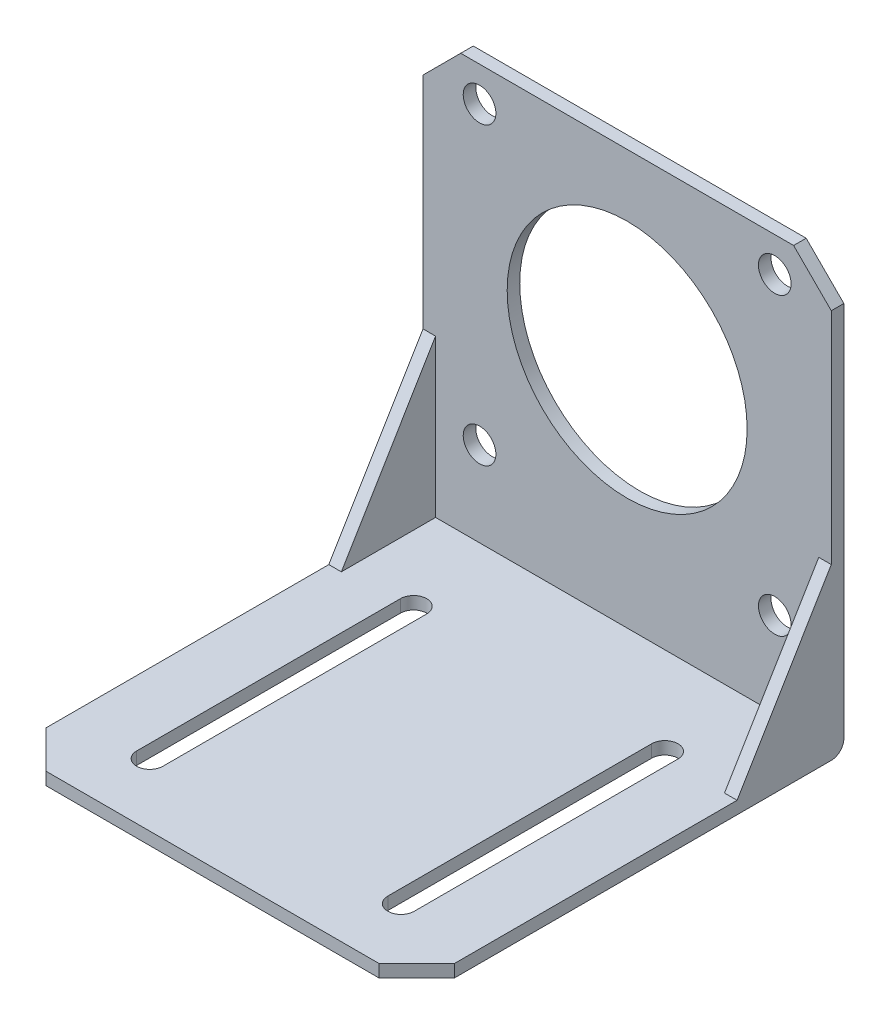
SolidWorks part; units mm, degrees
ref_plane "前视基准面" through (0, 0, 0) normal (0, 0, 1) x (1, 0, 0)
ref_plane "上视基准面" through (0, 0, 0) normal (0, 1, 0) x (1, 0, 0)
ref_plane "右视基准面" through (0, 0, 0) normal (1, 0, 0) x (0, 0, -1)
sketch "草图1" plane through (0, 0, 0) normal (1, 0, 0) x (0, 0, -1)
  line L0 (0, 0) -> (0, 68)
  line L1 (0, 68) -> (-2, 68)
  line L2 (-2, 68) -> (-2, 2)
  line L3 (-2, 2) -> (-68, 2)
  line L4 (-68, 2) -> (-68, 0)
  line L5 (-68, 0) -> (0, 0)
  line L6 (-17, 2) -> (-2, 27)
  dimension "D1" = 68
  dimension "D2" = 68
  dimension "D3" = 2
  dimension "D4" = 2
  dimension "D5" = 25
  dimension "D6" = 15
extrude "凸台-拉伸1" add sketch "草图1" along normal mid plane 65 contours L6 L3 L2
sketch "草图6" plane through (0, 0, 0) normal (1, 0, 0) x (0, 0, -1)
  line L0 (-17, 2) -> (-2, 27)
  line L1 (-2, 27) -> (-2, 2)
  line L2 (-2, 2) -> (-17, 2)
extrude "切除-拉伸3" cut sketch "草图6" against normal mid plane 61
sketch "草图7" plane through (0, 0, 0) normal (0, 1, 0) x (1, 0, 0)
  line L0 (-20, -16) -> (-20, -58) construction
  line L1 (-17.9, -16) -> (-17.9, -58)
  line L2 (-22.1, -16) -> (-22.1, -58)
  line L3 (32.5, -68) -> (-32.5, -68) construction
  line L5 (20, -16) -> (20, -58) construction
  line L6 (17.9, -16) -> (17.9, -58)
  line L7 (22.1, -16) -> (22.1, -58)
  arc A0 (-17.9, -16) -> (-22.1, -16) centre (-20, -16) ccw
  arc A1 (-22.1, -58) -> (-17.9, -58) centre (-20, -58) ccw
  arc A2 (17.9, -16) -> (22.1, -16) centre (20, -16) cw
  arc A3 (22.1, -58) -> (17.9, -58) centre (20, -58) cw
  point P2 (-20, -37)
  point P14 (20, -37)
  dimension "D2" = 2.1
  dimension "D1" = 42
  dimension "D3" = 20
  dimension "D4" = 10
extrude "凸台-拉伸2" add sketch "草图7" along normal through all contours L1 A1 L2 A0 | L6 A3 L7 A2
sketch "草图10" plane through (0, 0, 0) normal (0, 1, 0) x (1, 0, 0)
  line L0 (-20, -16) -> (-20, -58) construction
  line L1 (-17.9, -16) -> (-17.9, -58)
  line L2 (-22.1, -16) -> (-22.1, -58)
  line L4 (20, -16) -> (20, -58) construction
  line L5 (17.9, -16) -> (17.9, -58)
  line L6 (22.1, -16) -> (22.1, -58)
  arc A0 (-17.9, -16) -> (-22.1, -16) centre (-20, -16) ccw
  arc A1 (-22.1, -58) -> (-17.9, -58) centre (-20, -58) ccw
  arc A2 (17.9, -16) -> (22.1, -16) centre (20, -16) cw
  arc A3 (22.1, -58) -> (17.9, -58) centre (20, -58) cw
  point P4 (-20, -37)
  point P14 (20, -37)
  dimension "D1" = 2.1
extrude "切除-拉伸8" cut sketch "草图10" along normal through all
sketch "草图11" plane through (0, 0, 0) normal (0, 0, 1) x (1, 0, 0)
  line L0 (0, 0) -> (0, 12.9122)
  line L1 (32.5, 68) -> (32.5, 27) construction
  line L2 (32.5, 68) -> (-32.5, 68) construction
  line L3 (0, 39) -> (-23.5, 39)
  line L4 (-32.5, 68) -> (-32.5, 27) construction
  circle A0 centre (0, 39) radius 19.1
  circle A1 centre (-23.5, 62.5) radius 2.6
  circle A2 centre (23.5, 62.5) radius 2.6
  circle A3 centre (23.5, 15.5) radius 2.6
  circle A4 centre (-23.5, 15.5) radius 2.6
  point P23 (0, 39)
  dimension "D1" = 38.2
  dimension "D2" = 5.2
  dimension "D3" = 32.5
  dimension "D4" = 29
  dimension "D5" = 23.5
  dimension "D6" = 9
  dimension "D7" = 4
extrude "切除-拉伸10" cut sketch "草图11" along normal through all
chamfer "倒角1" distance 6 angle 45 1 edges at (-32.5, 68, 1)
chamfer "倒角2" distance 6 angle 45 1 edges at (32.5, 68, 1)
chamfer "倒角3" distance 6 angle 45 1 edges at (-32.5, 1, 68)
chamfer "倒角4" distance 6 angle 45 1 edges at (32.5, 1, 68)
fillet "圆角1" radius 2 1 edges at (0, 0, 0)
